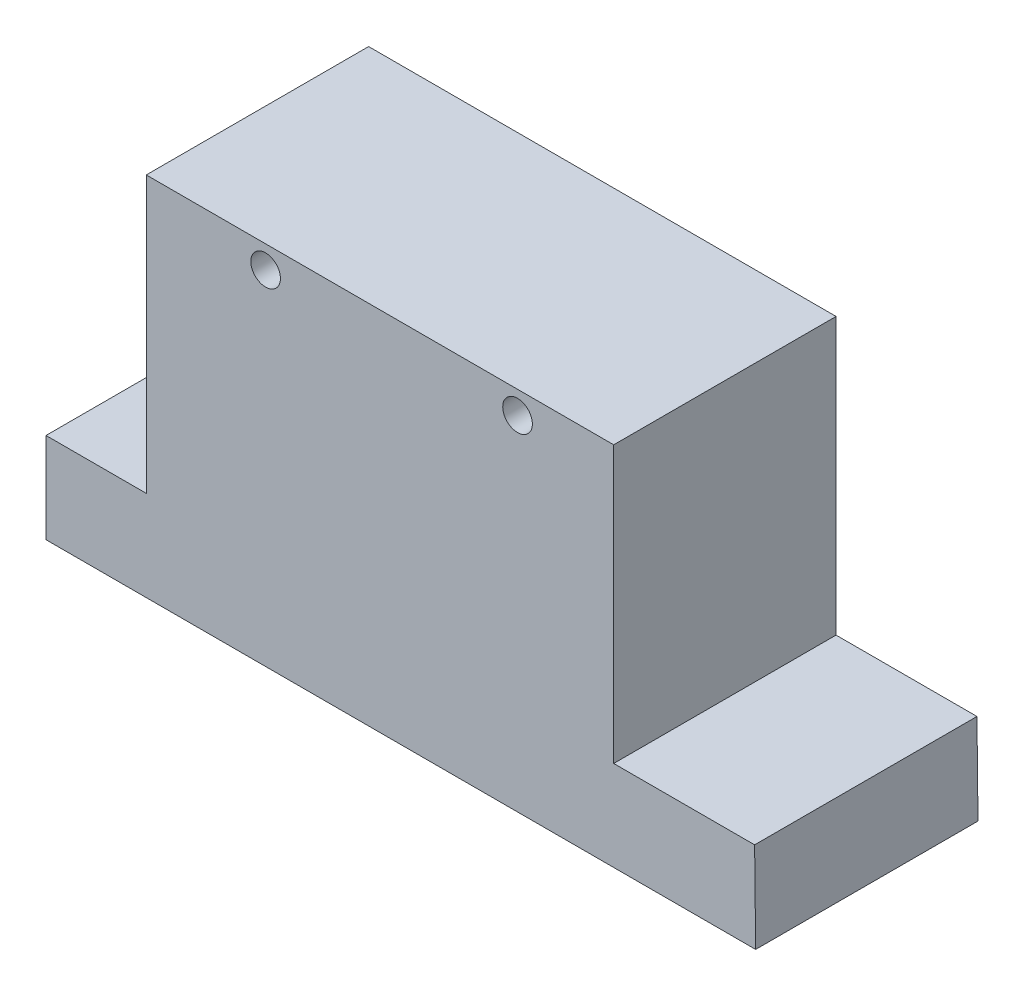
SolidWorks part; units mm, degrees
ref_plane "Front Plane" through (0, 0, 0) normal (0, 0, 1) x (1, 0, 0)
ref_plane "Top Plane" through (0, 0, 0) normal (0, 1, 0) x (1, 0, 0)
ref_plane "Right Plane" through (0, 0, 0) normal (1, 0, 0) x (0, 0, -1)
sketch "Sketch1" plane through (0, 0, 0) normal (0, 0, 1) x (1, 0, 0)
  line L0 (-78.4773, -6.7158) -> (-105.5344, -6.7158)
  line L2 (31.2766, -31.0847) -> (85.9646, -31.0847)
  line L3 (85.685, -6.7726) -> (85.9646, -31.0847)
  line L4 (47.6606, -6.7726) -> (85.685, -6.7726)
  line L5 (-105.5344, -6.7158) -> (-105.5344, -31.0847)
  line L6 (-55.8373, -31.0847) -> (-105.5344, -31.0847)
  line L7 (-78.4773, -6.7158) -> (-78.4773, 67.7011)
  line L8 (-78.4773, 67.7011) -> (47.6606, 67.7011)
  line L9 (-55.8373, -31.0847) -> (31.2766, -31.0847)
  line L10 (47.6606, -6.7726) -> (47.6606, 67.7011)
  circle A0 centre (-46.2714, 61.5865) radius 4
  circle A1 centre (21.7106, 61.5865) radius 4
  dimension "D1" = 90
  dimension "D2" = 90
extrude "Boss-Extrude1" add sketch "Sketch1" along normal blind 60
